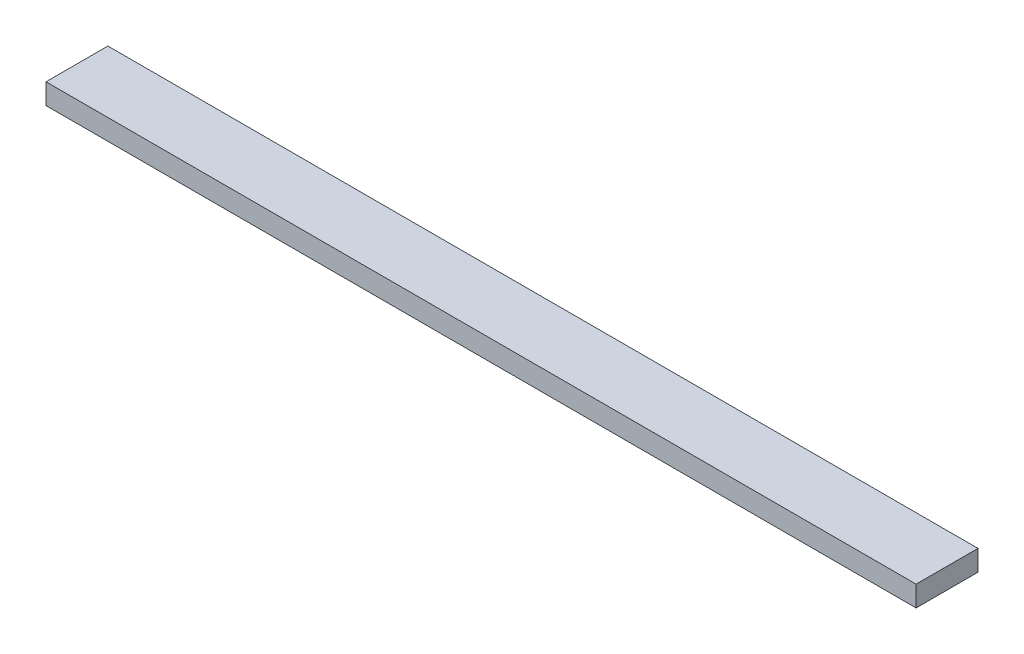
SolidWorks part; units mm, degrees
material "ABS"
ref_plane "Front Plane" through (0, 0, 0) normal (0, 0, 1) x (1, 0, 0)
ref_plane "Top Plane" through (0, 0, 0) normal (0, 1, 0) x (1, 0, 0)
ref_plane "Right Plane" through (0, 0, 0) normal (1, 0, 0) x (0, 0, -1)
sketch "Sketch1" plane through (0, 0, 0) normal (0, 0, 1) x (1, 0, 0)
  line L0 (5.5, 0) -> (-5.5, 0) construction
  line L1 (-77.8319, 4) -> (77.8319, 4)
  line L2 (-77.8319, 4) -> (-77.8319, 0)
  line L3 (-77.8319, 0) -> (77.8319, 0)
  line L4 (77.8319, 4) -> (77.8319, 0)
  line L5 (0, -9.2078) -> (0, 9.2078) construction
extrude "Boss-Extrude1" add sketch "Sketch1" along normal blind 10
sketch "Sketch2" plane through (0, 0, 0) normal (0, 0, 1) x (1, 0, 0)
  line L0 (-65.3126, 4) -> (-63.6747, 8.5)
  line L1 (77.8319, 4) -> (-77.8319, 4) construction
  line L2 (-63.6747, 8.5) -> (-61.989, 8.5)
  line L3 (-61.989, 8.5) -> (-60.3511, 4)
  line L4 (-65.3126, 4) -> (-60.3511, 4)
  line L5 (0, -9.2078) -> (0, 9.2078) construction
  line L6 (-62.8319, 8.5) -> (-62.8319, 4) construction
  line L9 (-34.7801, 6.5) -> (34.9733, 6.5) construction
  point P18 (-61.2611, 6.5)
  point P19 (-64.4026, 6.5)
extrude "Boss-Extrude4" add sketch "Sketch2" along normal up to surface (10 mm away) up to face at (0, 2, 10)
fillet "Fillet1" radius 0.5 2 edges
pattern_linear "LPattern1" count 21 spacing 6.2832 along (1, 0, 0) of "Boss-Extrude4", "Fillet1"
hole_wizard "CSK for M4 Hex Socket Countersunk Cap Screw1" positions "Sketch7" profile "Sketch6" countersink size "M4" standard "ISO"
sketch "Sketch7" plane through (0, 4, 0) normal (0, 1, 0) x (1, 0, 0)
  line L0 (-77.8319, -10) -> (-77.8319, 0) construction
  line L1 (77.8319, -10) -> (77.8319, 0) construction
  line L2 (-4.5728, 0) -> (4.5728, 0) construction
  point P0 (-71.8319, -5)
  point P2 (71.8319, -5)
sketch "Sketch6" plane through (-71.8319, 4, 5) normal (1, 0, 0) x (0, 0, 1)
  line L0 (0, 0) -> (0, 4)
  line L1 (0, 4) -> (2.25, 4)
  line L2 (2.25, 4) -> (2.25, 2.23)
  line L3 (2.25, 2.23) -> (4.48, 0)
  line L5 (4.48, 0) -> (0, 0)
  line L6 (-2.25, 2.23) -> (-4.48, 0) construction
  line L11 (0, -6.35) -> (0, 107.95) construction
  dimension "Thru Hole Dia." = 4.5
  dimension "Thru Hole Depth" = 4
  dimension "Near C'Sink Dia." = 8.96
  dimension "Near C'Sink Angle" = 90
ref_plane "Plane1" through (0, 26.5, 0) normal (0, 1, 0) x (1, 0, 0)
sketch "Sketch8" [suppressed] plane through (0, 0, 0) normal (0, -1, 0) x (1, 0, 0)
  line L4 (-77.8319, 0) -> (77.8319, 0)
  line L5 (77.8319, 0) -> (77.8319, 10)
  line L6 (77.8319, 10) -> (-77.8319, 10)
  line L7 (-77.8319, 10) -> (-77.8319, 0)
  line L8 (-77.8319, 0) -> (77.8319, 0)
  line L9 (77.8319, 0) -> (77.8319, 10)
  line L10 (77.8319, 10) -> (-77.8319, 10)
  line L11 (-77.8319, 10) -> (-77.8319, 0)
  circle A0 centre (-71.8319, 5) radius 2.25 construction
  circle A1 centre (-71.8319, 5) radius 2.25
  dimension "D1" = 0
extrude "Boss-Extrude5" [suppressed] add sketch "Sketch8" along normal blind 30
sketch "Sketch9" plane through (0, 0, 10) normal (0, 0, 1) x (1, 0, 0)
  line L88 (-77.8319, 4) -> (-77.8319, 0)
  line L89 (-77.8319, 0) -> (77.8319, 0)
  line L90 (-77.8319, 4) -> (-77.8319, 0)
  line L91 (77.8319, 4) -> (65.6627, 4)
  line L92 (65.1928, 4.329) -> (63.6747, 8.5)
  line L93 (63.6747, 8.5) -> (61.989, 8.5)
  line L94 (61.989, 8.5) -> (60.4709, 4.329)
  line L95 (60.001, 4) -> (59.3795, 4)
  line L96 (58.9096, 4.329) -> (57.3915, 8.5)
  line L97 (57.3915, 8.5) -> (55.7058, 8.5)
  line L98 (55.7058, 8.5) -> (54.1877, 4.329)
  line L99 (53.7178, 4) -> (53.0963, 4)
  line L100 (52.6265, 4.329) -> (51.1083, 8.5)
  line L101 (51.1083, 8.5) -> (49.4226, 8.5)
  line L102 (49.4226, 8.5) -> (47.9045, 4.329)
  line L103 (47.4347, 4) -> (46.8131, 4)
  line L104 (46.3433, 4.329) -> (44.8252, 8.5)
  line L105 (44.8252, 8.5) -> (43.1394, 8.5)
  line L106 (43.1394, 8.5) -> (41.6213, 4.329)
  line L107 (41.1515, 4) -> (40.5299, 4)
  line L108 (40.0601, 4.329) -> (38.542, 8.5)
  line L109 (38.542, 8.5) -> (36.8563, 8.5)
  line L110 (36.8563, 8.5) -> (35.3381, 4.329)
  line L111 (34.8683, 4) -> (34.2468, 4)
  line L112 (33.7769, 4.329) -> (32.2588, 8.5)
  line L113 (32.2588, 8.5) -> (30.5731, 8.5)
  line L114 (30.5731, 8.5) -> (29.0549, 4.329)
  line L115 (28.5851, 4) -> (27.9636, 4)
  line L116 (27.4937, 4.329) -> (25.9756, 8.5)
  line L117 (25.9756, 8.5) -> (24.2899, 8.5)
  line L118 (24.2899, 8.5) -> (22.7718, 4.329)
  line L119 (22.3019, 4) -> (21.6804, 4)
  line L120 (21.2105, 4.329) -> (19.6924, 8.5)
  line L121 (19.6924, 8.5) -> (18.0067, 8.5)
  line L122 (18.0067, 8.5) -> (16.4886, 4.329)
  line L123 (16.0187, 4) -> (15.3972, 4)
  line L124 (14.9273, 4.329) -> (13.4092, 8.5)
  line L125 (13.4092, 8.5) -> (11.7235, 8.5)
  line L126 (11.7235, 8.5) -> (10.2054, 4.329)
  line L127 (9.7355, 4) -> (9.114, 4)
  line L128 (8.6442, 4.329) -> (7.126, 8.5)
  line L129 (7.126, 8.5) -> (5.4403, 8.5)
  line L130 (5.4403, 8.5) -> (3.9222, 4.329)
  line L131 (3.4524, 4) -> (2.8308, 4)
  line L132 (2.361, 4.329) -> (0.8429, 8.5)
  line L133 (0.8429, 8.5) -> (-0.8429, 8.5)
  line L134 (-0.8429, 8.5) -> (-2.361, 4.329)
  line L135 (-2.8308, 4) -> (-3.4524, 4)
  line L136 (-3.9222, 4.329) -> (-5.4403, 8.5)
  line L137 (-5.4403, 8.5) -> (-7.126, 8.5)
  line L138 (-7.126, 8.5) -> (-8.6442, 4.329)
  line L139 (-9.114, 4) -> (-9.7355, 4)
  line L140 (-10.2054, 4.329) -> (-11.7235, 8.5)
  line L141 (-11.7235, 8.5) -> (-13.4092, 8.5)
  line L142 (-13.4092, 8.5) -> (-14.9273, 4.329)
  line L143 (-15.3972, 4) -> (-16.0187, 4)
  line L144 (-16.4886, 4.329) -> (-18.0067, 8.5)
  line L145 (-18.0067, 8.5) -> (-19.6924, 8.5)
  line L146 (-19.6924, 8.5) -> (-21.2105, 4.329)
  line L147 (-21.6804, 4) -> (-22.3019, 4)
  line L148 (-22.7718, 4.329) -> (-24.2899, 8.5)
  line L149 (-24.2899, 8.5) -> (-25.9756, 8.5)
  line L150 (-25.9756, 8.5) -> (-27.4937, 4.329)
  line L151 (-27.9636, 4) -> (-28.5851, 4)
  line L152 (-29.0549, 4.329) -> (-30.5731, 8.5)
  line L153 (-30.5731, 8.5) -> (-32.2588, 8.5)
  line L154 (-32.2588, 8.5) -> (-33.7769, 4.329)
  line L155 (-34.2468, 4) -> (-34.8683, 4)
  line L156 (-35.3381, 4.329) -> (-36.8563, 8.5)
  line L157 (-36.8563, 8.5) -> (-38.542, 8.5)
  line L158 (-38.542, 8.5) -> (-40.0601, 4.329)
  line L159 (-40.5299, 4) -> (-41.1515, 4)
  line L160 (-41.6213, 4.329) -> (-43.1394, 8.5)
  line L161 (-43.1394, 8.5) -> (-44.8252, 8.5)
  line L162 (-44.8252, 8.5) -> (-46.3433, 4.329)
  line L163 (-46.8131, 4) -> (-47.4347, 4)
  line L164 (-47.9045, 4.329) -> (-49.4226, 8.5)
  line L165 (-49.4226, 8.5) -> (-51.1083, 8.5)
  line L166 (-51.1083, 8.5) -> (-52.6265, 4.329)
  line L167 (-53.0963, 4) -> (-53.7178, 4)
  line L168 (-54.1877, 4.329) -> (-55.7058, 8.5)
  line L169 (-55.7058, 8.5) -> (-57.3915, 8.5)
  line L170 (-57.3915, 8.5) -> (-58.9096, 4.329)
  line L171 (-59.3795, 4) -> (-60.001, 4)
  line L172 (-60.4709, 4.329) -> (-61.989, 8.5)
  line L173 (-61.989, 8.5) -> (-63.6747, 8.5)
  line L174 (-63.6747, 8.5) -> (-65.1928, 4.329)
  line L175 (-65.6627, 4) -> (-77.8319, 4)
  line L176 (77.8319, 0) -> (77.8319, 4)
  line L177 (-77.8319, 0) -> (77.8319, 0)
  line L178 (77.8319, 0) -> (77.8319, 4)
  line L179 (77.8319, 4) -> (65.6627, 4)
  line L180 (65.1928, 4.329) -> (63.6747, 8.5)
  line L181 (63.6747, 8.5) -> (61.989, 8.5)
  line L182 (61.989, 8.5) -> (60.4709, 4.329)
  line L183 (60.001, 4) -> (59.3795, 4)
  line L184 (58.9096, 4.329) -> (57.3915, 8.5)
  line L185 (57.3915, 8.5) -> (55.7058, 8.5)
  line L186 (55.7058, 8.5) -> (54.1877, 4.329)
  line L187 (53.7178, 4) -> (53.0963, 4)
  line L188 (52.6265, 4.329) -> (51.1083, 8.5)
  line L189 (51.1083, 8.5) -> (49.4226, 8.5)
  line L190 (49.4226, 8.5) -> (47.9045, 4.329)
  line L191 (47.4347, 4) -> (46.8131, 4)
  line L192 (46.3433, 4.329) -> (44.8252, 8.5)
  line L193 (44.8252, 8.5) -> (43.1394, 8.5)
  line L194 (43.1394, 8.5) -> (41.6213, 4.329)
  line L195 (41.1515, 4) -> (40.5299, 4)
  line L196 (40.0601, 4.329) -> (38.542, 8.5)
  line L197 (38.542, 8.5) -> (36.8563, 8.5)
  line L198 (36.8563, 8.5) -> (35.3381, 4.329)
  line L199 (34.8683, 4) -> (34.2468, 4)
  line L200 (33.7769, 4.329) -> (32.2588, 8.5)
  line L201 (32.2588, 8.5) -> (30.5731, 8.5)
  line L202 (30.5731, 8.5) -> (29.0549, 4.329)
  line L203 (28.5851, 4) -> (27.9636, 4)
  line L204 (27.4937, 4.329) -> (25.9756, 8.5)
  line L205 (25.9756, 8.5) -> (24.2899, 8.5)
  line L206 (24.2899, 8.5) -> (22.7718, 4.329)
  line L207 (22.3019, 4) -> (21.6804, 4)
  line L208 (21.2105, 4.329) -> (19.6924, 8.5)
  line L209 (19.6924, 8.5) -> (18.0067, 8.5)
  line L210 (18.0067, 8.5) -> (16.4886, 4.329)
  line L211 (16.0187, 4) -> (15.3972, 4)
  line L212 (14.9273, 4.329) -> (13.4092, 8.5)
  line L213 (13.4092, 8.5) -> (11.7235, 8.5)
  line L214 (11.7235, 8.5) -> (10.2054, 4.329)
  line L215 (9.7355, 4) -> (9.114, 4)
  line L216 (8.6442, 4.329) -> (7.126, 8.5)
  line L217 (7.126, 8.5) -> (5.4403, 8.5)
  line L218 (5.4403, 8.5) -> (3.9222, 4.329)
  line L219 (3.4524, 4) -> (2.8308, 4)
  line L220 (2.361, 4.329) -> (0.8429, 8.5)
  line L221 (0.8429, 8.5) -> (-0.8429, 8.5)
  line L222 (-0.8429, 8.5) -> (-2.361, 4.329)
  line L223 (-2.8308, 4) -> (-3.4524, 4)
  line L224 (-3.9222, 4.329) -> (-5.4403, 8.5)
  line L225 (-5.4403, 8.5) -> (-7.126, 8.5)
  line L226 (-7.126, 8.5) -> (-8.6442, 4.329)
  line L227 (-9.114, 4) -> (-9.7355, 4)
  line L228 (-10.2054, 4.329) -> (-11.7235, 8.5)
  line L229 (-11.7235, 8.5) -> (-13.4092, 8.5)
  line L230 (-13.4092, 8.5) -> (-14.9273, 4.329)
  line L231 (-15.3972, 4) -> (-16.0187, 4)
  line L232 (-16.4886, 4.329) -> (-18.0067, 8.5)
  line L233 (-18.0067, 8.5) -> (-19.6924, 8.5)
  line L234 (-19.6924, 8.5) -> (-21.2105, 4.329)
  line L235 (-21.6804, 4) -> (-22.3019, 4)
  line L236 (-22.7718, 4.329) -> (-24.2899, 8.5)
  line L237 (-24.2899, 8.5) -> (-25.9756, 8.5)
  line L238 (-25.9756, 8.5) -> (-27.4937, 4.329)
  line L239 (-27.9636, 4) -> (-28.5851, 4)
  line L240 (-29.0549, 4.329) -> (-30.5731, 8.5)
  line L241 (-30.5731, 8.5) -> (-32.2588, 8.5)
  line L242 (-32.2588, 8.5) -> (-33.7769, 4.329)
  line L243 (-34.2468, 4) -> (-34.8683, 4)
  line L244 (-35.3381, 4.329) -> (-36.8563, 8.5)
  line L245 (-36.8563, 8.5) -> (-38.542, 8.5)
  line L246 (-38.542, 8.5) -> (-40.0601, 4.329)
  line L247 (-40.5299, 4) -> (-41.1515, 4)
  line L248 (-41.6213, 4.329) -> (-43.1394, 8.5)
  line L249 (-43.1394, 8.5) -> (-44.8252, 8.5)
  line L250 (-44.8252, 8.5) -> (-46.3433, 4.329)
  line L251 (-46.8131, 4) -> (-47.4347, 4)
  line L252 (-47.9045, 4.329) -> (-49.4226, 8.5)
  line L253 (-49.4226, 8.5) -> (-51.1083, 8.5)
  line L254 (-51.1083, 8.5) -> (-52.6265, 4.329)
  line L255 (-53.0963, 4) -> (-53.7178, 4)
  line L256 (-54.1877, 4.329) -> (-55.7058, 8.5)
  line L257 (-55.7058, 8.5) -> (-57.3915, 8.5)
  line L258 (-57.3915, 8.5) -> (-58.9096, 4.329)
  line L259 (-59.3795, 4) -> (-60.001, 4)
  line L260 (-60.4709, 4.329) -> (-61.989, 8.5)
  line L261 (-61.989, 8.5) -> (-63.6747, 8.5)
  line L262 (-63.6747, 8.5) -> (-65.1928, 4.329)
  line L263 (-65.6627, 4) -> (-77.8319, 4)
  arc A42 (65.1928, 4.329) -> (65.6627, 4) centre (65.6627, 4.5) ccw
  arc A43 (60.001, 4) -> (60.4709, 4.329) centre (60.001, 4.5) ccw
  arc A44 (58.9096, 4.329) -> (59.3795, 4) centre (59.3795, 4.5) ccw
  arc A45 (53.7178, 4) -> (54.1877, 4.329) centre (53.7178, 4.5) ccw
  arc A46 (52.6265, 4.329) -> (53.0963, 4) centre (53.0963, 4.5) ccw
  arc A47 (47.4347, 4) -> (47.9045, 4.329) centre (47.4347, 4.5) ccw
  arc A48 (46.3433, 4.329) -> (46.8131, 4) centre (46.8131, 4.5) ccw
  arc A49 (41.1515, 4) -> (41.6213, 4.329) centre (41.1515, 4.5) ccw
  arc A50 (40.0601, 4.329) -> (40.5299, 4) centre (40.5299, 4.5) ccw
  arc A51 (34.8683, 4) -> (35.3381, 4.329) centre (34.8683, 4.5) ccw
  arc A52 (33.7769, 4.329) -> (34.2468, 4) centre (34.2468, 4.5) ccw
  arc A53 (28.5851, 4) -> (29.0549, 4.329) centre (28.5851, 4.5) ccw
  arc A54 (27.4937, 4.329) -> (27.9636, 4) centre (27.9636, 4.5) ccw
  arc A55 (22.3019, 4) -> (22.7718, 4.329) centre (22.3019, 4.5) ccw
  arc A56 (21.2105, 4.329) -> (21.6804, 4) centre (21.6804, 4.5) ccw
  arc A57 (16.0187, 4) -> (16.4886, 4.329) centre (16.0187, 4.5) ccw
  arc A58 (14.9273, 4.329) -> (15.3972, 4) centre (15.3972, 4.5) ccw
  arc A59 (9.7355, 4) -> (10.2054, 4.329) centre (9.7355, 4.5) ccw
  arc A60 (8.6442, 4.329) -> (9.114, 4) centre (9.114, 4.5) ccw
  arc A61 (3.4524, 4) -> (3.9222, 4.329) centre (3.4524, 4.5) ccw
  arc A62 (2.361, 4.329) -> (2.8308, 4) centre (2.8308, 4.5) ccw
  arc A63 (-2.8308, 4) -> (-2.361, 4.329) centre (-2.8308, 4.5) ccw
  arc A64 (-3.9222, 4.329) -> (-3.4524, 4) centre (-3.4524, 4.5) ccw
  arc A65 (-9.114, 4) -> (-8.6442, 4.329) centre (-9.114, 4.5) ccw
  arc A66 (-10.2054, 4.329) -> (-9.7355, 4) centre (-9.7355, 4.5) ccw
  arc A67 (-15.3972, 4) -> (-14.9273, 4.329) centre (-15.3972, 4.5) ccw
  arc A68 (-16.4886, 4.329) -> (-16.0187, 4) centre (-16.0187, 4.5) ccw
  arc A69 (-21.6804, 4) -> (-21.2105, 4.329) centre (-21.6804, 4.5) ccw
  arc A70 (-22.7718, 4.329) -> (-22.3019, 4) centre (-22.3019, 4.5) ccw
  arc A71 (-27.9636, 4) -> (-27.4937, 4.329) centre (-27.9636, 4.5) ccw
  arc A72 (-29.0549, 4.329) -> (-28.5851, 4) centre (-28.5851, 4.5) ccw
  arc A73 (-34.2468, 4) -> (-33.7769, 4.329) centre (-34.2468, 4.5) ccw
  arc A74 (-35.3381, 4.329) -> (-34.8683, 4) centre (-34.8683, 4.5) ccw
  arc A75 (-40.5299, 4) -> (-40.0601, 4.329) centre (-40.5299, 4.5) ccw
  arc A76 (-41.6213, 4.329) -> (-41.1515, 4) centre (-41.1515, 4.5) ccw
  arc A77 (-46.8131, 4) -> (-46.3433, 4.329) centre (-46.8131, 4.5) ccw
  arc A78 (-47.9045, 4.329) -> (-47.4347, 4) centre (-47.4347, 4.5) ccw
  arc A79 (-53.0963, 4) -> (-52.6265, 4.329) centre (-53.0963, 4.5) ccw
  arc A80 (-54.1877, 4.329) -> (-53.7178, 4) centre (-53.7178, 4.5) ccw
  arc A81 (-59.3795, 4) -> (-58.9096, 4.329) centre (-59.3795, 4.5) ccw
  arc A82 (-60.4709, 4.329) -> (-60.001, 4) centre (-60.001, 4.5) ccw
  arc A83 (-65.6627, 4) -> (-65.1928, 4.329) centre (-65.6627, 4.5) ccw
  arc A84 (65.1928, 4.329) -> (65.6627, 4) centre (65.6627, 4.5) ccw
  arc A85 (60.001, 4) -> (60.4709, 4.329) centre (60.001, 4.5) ccw
  arc A86 (58.9096, 4.329) -> (59.3795, 4) centre (59.3795, 4.5) ccw
  arc A87 (53.7178, 4) -> (54.1877, 4.329) centre (53.7178, 4.5) ccw
  arc A88 (52.6265, 4.329) -> (53.0963, 4) centre (53.0963, 4.5) ccw
  arc A89 (47.4347, 4) -> (47.9045, 4.329) centre (47.4347, 4.5) ccw
  arc A90 (46.3433, 4.329) -> (46.8131, 4) centre (46.8131, 4.5) ccw
  arc A91 (41.1515, 4) -> (41.6213, 4.329) centre (41.1515, 4.5) ccw
  arc A92 (40.0601, 4.329) -> (40.5299, 4) centre (40.5299, 4.5) ccw
  arc A93 (34.8683, 4) -> (35.3381, 4.329) centre (34.8683, 4.5) ccw
  arc A94 (33.7769, 4.329) -> (34.2468, 4) centre (34.2468, 4.5) ccw
  arc A95 (28.5851, 4) -> (29.0549, 4.329) centre (28.5851, 4.5) ccw
  arc A96 (27.4937, 4.329) -> (27.9636, 4) centre (27.9636, 4.5) ccw
  arc A97 (22.3019, 4) -> (22.7718, 4.329) centre (22.3019, 4.5) ccw
  arc A98 (21.2105, 4.329) -> (21.6804, 4) centre (21.6804, 4.5) ccw
  arc A99 (16.0187, 4) -> (16.4886, 4.329) centre (16.0187, 4.5) ccw
  arc A100 (14.9273, 4.329) -> (15.3972, 4) centre (15.3972, 4.5) ccw
  arc A101 (9.7355, 4) -> (10.2054, 4.329) centre (9.7355, 4.5) ccw
  arc A102 (8.6442, 4.329) -> (9.114, 4) centre (9.114, 4.5) ccw
  arc A103 (3.4524, 4) -> (3.9222, 4.329) centre (3.4524, 4.5) ccw
  arc A104 (2.361, 4.329) -> (2.8308, 4) centre (2.8308, 4.5) ccw
  arc A105 (-2.8308, 4) -> (-2.361, 4.329) centre (-2.8308, 4.5) ccw
  arc A106 (-3.9222, 4.329) -> (-3.4524, 4) centre (-3.4524, 4.5) ccw
  arc A107 (-9.114, 4) -> (-8.6442, 4.329) centre (-9.114, 4.5) ccw
  arc A108 (-10.2054, 4.329) -> (-9.7355, 4) centre (-9.7355, 4.5) ccw
  arc A109 (-15.3972, 4) -> (-14.9273, 4.329) centre (-15.3972, 4.5) ccw
  arc A110 (-16.4886, 4.329) -> (-16.0187, 4) centre (-16.0187, 4.5) ccw
  arc A111 (-21.6804, 4) -> (-21.2105, 4.329) centre (-21.6804, 4.5) ccw
  arc A112 (-22.7718, 4.329) -> (-22.3019, 4) centre (-22.3019, 4.5) ccw
  arc A113 (-27.9636, 4) -> (-27.4937, 4.329) centre (-27.9636, 4.5) ccw
  arc A114 (-29.0549, 4.329) -> (-28.5851, 4) centre (-28.5851, 4.5) ccw
  arc A115 (-34.2468, 4) -> (-33.7769, 4.329) centre (-34.2468, 4.5) ccw
  arc A116 (-35.3381, 4.329) -> (-34.8683, 4) centre (-34.8683, 4.5) ccw
  arc A117 (-40.5299, 4) -> (-40.0601, 4.329) centre (-40.5299, 4.5) ccw
  arc A118 (-41.6213, 4.329) -> (-41.1515, 4) centre (-41.1515, 4.5) ccw
  arc A119 (-46.8131, 4) -> (-46.3433, 4.329) centre (-46.8131, 4.5) ccw
  arc A120 (-47.9045, 4.329) -> (-47.4347, 4) centre (-47.4347, 4.5) ccw
  arc A121 (-53.0963, 4) -> (-52.6265, 4.329) centre (-53.0963, 4.5) ccw
  arc A122 (-54.1877, 4.329) -> (-53.7178, 4) centre (-53.7178, 4.5) ccw
  arc A123 (-59.3795, 4) -> (-58.9096, 4.329) centre (-59.3795, 4.5) ccw
  arc A124 (-60.4709, 4.329) -> (-60.001, 4) centre (-60.001, 4.5) ccw
  arc A125 (-65.6627, 4) -> (-65.1928, 4.329) centre (-65.6627, 4.5) ccw
  dimension "D1" = 0
extrude "Boss-Extrude6" add sketch "Sketch9" along normal blind 6 contours L262 A125 L263 L90 L177 L178 L179 A84 L180 L181 L182 A85 L183 A86 L184 L185 L186 A87 L187 A88 L188 L189 L190 A89 L191 A90 L192 L193 L194 A91 L195 A92 L196 L197 L198 A93 L199 A94 L200 L201 L202 A95 L203 A96 L204 L205 L206 A97 L207 A98 L208 L209 L210 A99 L211 A100 L212 L213 L214 A101 L215 A102 L216 L217 L218 A103 L219 A104 L220 L221 L222 A105 L223 A106 L224 L225 L226 A107 L227 A108 L228 L229 L230 A109 L231 A110 L232 L233 L234 A111 L235 A112 L236 L237 L238 A113 L239 A114 L240 L241 L242 A115 L243 A116 L244 L245 L246 A117 L247 A118 L248 L249 L250 A119 L251 A120 L252 L253 L254 A121 L255 A122 L256 L257 L258 A123 L259 A124 L260 L261
sketch "Sketch10" [suppressed] plane through (0, 0, 16) normal (0, 0, 1) x (1, 0, 0)
  line L0 (-49.4226, 8.5) -> (-51.1083, 8.5) construction
  line L1 (-77.8319, -30) -> (90.1846, -30)
  line L2 (-77.8319, -30) -> (-77.8319, -7.5)
  line L3 (-77.8319, -7.5) -> (90.1846, -7.5)
  line L4 (90.1846, -30) -> (90.1846, -7.5)
  dimension "D1" = 16
extrude "Cut-Extrude1" [suppressed] cut sketch "Sketch10" against normal blind 40
sketch "Sketch11" plane through (-77.8319, 0, 0) normal (-1, 0, 0) x (0, 0, 1)
  line L4 (0, 4) -> (0, 0)
  line L5 (0, 0) -> (16, 0)
  line L6 (16, 0) -> (16, 4)
  line L7 (16, 4) -> (0, 4)
  line L8 (0, 4) -> (0, 0)
  line L9 (0, 0) -> (16, 0)
  line L10 (16, 0) -> (16, 4)
  line L11 (16, 4) -> (0, 4)
  dimension "D1" = 0
extrude "Boss-Extrude8" add sketch "Sketch11" along normal blind 10
sketch "Sketch12" plane through (77.8319, 0, 0) normal (1, 0, 0) x (0, 0, -1)
  line L4 (-16, 4) -> (-16, 0)
  line L5 (-16, 0) -> (0, 0)
  line L6 (0, 0) -> (0, 4)
  line L7 (0, 4) -> (-16, 4)
  line L8 (-16, 4) -> (-16, 0)
  line L9 (-16, 0) -> (0, 0)
  line L10 (0, 0) -> (0, 4)
  line L11 (0, 4) -> (-16, 4)
  dimension "D1" = 0
extrude "Boss-Extrude9" add sketch "Sketch12" along normal blind 10
sketch "Sketch15" plane through (0, 0, 0) normal (0, -1, 0) x (1, 0, 0)
  line L4 (-87.8319, 0) -> (87.8319, 0)
  line L5 (87.8319, 0) -> (87.8319, 16)
  line L6 (87.8319, 16) -> (-87.8319, 16)
  line L7 (-87.8319, 16) -> (-87.8319, 0)
  line L8 (-87.8319, 0) -> (87.8319, 0)
  line L9 (87.8319, 0) -> (87.8319, 16)
  line L10 (87.8319, 16) -> (-87.8319, 16)
  line L11 (-87.8319, 16) -> (-87.8319, 0)
  dimension "D1" = 0
extrude "Boss-Extrude10" add sketch "Sketch15" along normal blind 5
sketch "Sketch16" plane through (0, 0, 16) normal (0, 0, 1) x (1, 0, 0)
  line L88 (-61.989, 8.5) -> (-63.6747, 8.5)
  line L89 (-63.6747, 8.5) -> (-65.1928, 4.329)
  line L90 (-65.6627, 4) -> (-87.8319, 4)
  line L91 (-87.8319, 4) -> (-87.8319, -5)
  line L92 (-87.8319, -5) -> (87.8319, -5)
  line L93 (87.8319, -5) -> (87.8319, 4)
  line L94 (87.8319, 4) -> (65.6627, 4)
  line L95 (65.1928, 4.329) -> (63.6747, 8.5)
  line L96 (63.6747, 8.5) -> (61.989, 8.5)
  line L97 (61.989, 8.5) -> (60.4709, 4.329)
  line L98 (60.001, 4) -> (59.3795, 4)
  line L99 (58.9096, 4.329) -> (57.3915, 8.5)
  line L100 (57.3915, 8.5) -> (55.7058, 8.5)
  line L101 (55.7058, 8.5) -> (54.1877, 4.329)
  line L102 (53.7178, 4) -> (53.0963, 4)
  line L103 (52.6265, 4.329) -> (51.1083, 8.5)
  line L104 (51.1083, 8.5) -> (49.4226, 8.5)
  line L105 (49.4226, 8.5) -> (47.9045, 4.329)
  line L106 (47.4347, 4) -> (46.8131, 4)
  line L107 (46.3433, 4.329) -> (44.8252, 8.5)
  line L108 (44.8252, 8.5) -> (43.1394, 8.5)
  line L109 (43.1394, 8.5) -> (41.6213, 4.329)
  line L110 (41.1515, 4) -> (40.5299, 4)
  line L111 (40.0601, 4.329) -> (38.542, 8.5)
  line L112 (38.542, 8.5) -> (36.8563, 8.5)
  line L113 (36.8563, 8.5) -> (35.3381, 4.329)
  line L114 (34.8683, 4) -> (34.2468, 4)
  line L115 (33.7769, 4.329) -> (32.2588, 8.5)
  line L116 (32.2588, 8.5) -> (30.5731, 8.5)
  line L117 (30.5731, 8.5) -> (29.0549, 4.329)
  line L118 (28.5851, 4) -> (27.9636, 4)
  line L119 (27.4937, 4.329) -> (25.9756, 8.5)
  line L120 (25.9756, 8.5) -> (24.2899, 8.5)
  line L121 (24.2899, 8.5) -> (22.7718, 4.329)
  line L122 (22.3019, 4) -> (21.6804, 4)
  line L123 (21.2105, 4.329) -> (19.6924, 8.5)
  line L124 (19.6924, 8.5) -> (18.0067, 8.5)
  line L125 (18.0067, 8.5) -> (16.4886, 4.329)
  line L126 (16.0187, 4) -> (15.3972, 4)
  line L127 (14.9273, 4.329) -> (13.4092, 8.5)
  line L128 (13.4092, 8.5) -> (11.7235, 8.5)
  line L129 (11.7235, 8.5) -> (10.2054, 4.329)
  line L130 (9.7355, 4) -> (9.114, 4)
  line L131 (8.6442, 4.329) -> (7.126, 8.5)
  line L132 (7.126, 8.5) -> (5.4403, 8.5)
  line L133 (5.4403, 8.5) -> (3.9222, 4.329)
  line L134 (3.4524, 4) -> (2.8308, 4)
  line L135 (2.361, 4.329) -> (0.8429, 8.5)
  line L136 (0.8429, 8.5) -> (-0.8429, 8.5)
  line L137 (-0.8429, 8.5) -> (-2.361, 4.329)
  line L138 (-2.8308, 4) -> (-3.4524, 4)
  line L139 (-3.9222, 4.329) -> (-5.4403, 8.5)
  line L140 (-5.4403, 8.5) -> (-7.126, 8.5)
  line L141 (-7.126, 8.5) -> (-8.6442, 4.329)
  line L142 (-9.114, 4) -> (-9.7355, 4)
  line L143 (-10.2054, 4.329) -> (-11.7235, 8.5)
  line L144 (-11.7235, 8.5) -> (-13.4092, 8.5)
  line L145 (-13.4092, 8.5) -> (-14.9273, 4.329)
  line L146 (-15.3972, 4) -> (-16.0187, 4)
  line L147 (-16.4886, 4.329) -> (-18.0067, 8.5)
  line L148 (-18.0067, 8.5) -> (-19.6924, 8.5)
  line L149 (-19.6924, 8.5) -> (-21.2105, 4.329)
  line L150 (-21.6804, 4) -> (-22.3019, 4)
  line L151 (-22.7718, 4.329) -> (-24.2899, 8.5)
  line L152 (-24.2899, 8.5) -> (-25.9756, 8.5)
  line L153 (-25.9756, 8.5) -> (-27.4937, 4.329)
  line L154 (-27.9636, 4) -> (-28.5851, 4)
  line L155 (-29.0549, 4.329) -> (-30.5731, 8.5)
  line L156 (-30.5731, 8.5) -> (-32.2588, 8.5)
  line L157 (-32.2588, 8.5) -> (-33.7769, 4.329)
  line L158 (-34.2468, 4) -> (-34.8683, 4)
  line L159 (-35.3381, 4.329) -> (-36.8563, 8.5)
  line L160 (-36.8563, 8.5) -> (-38.542, 8.5)
  line L161 (-38.542, 8.5) -> (-40.0601, 4.329)
  line L162 (-40.5299, 4) -> (-41.1515, 4)
  line L163 (-41.6213, 4.329) -> (-43.1394, 8.5)
  line L164 (-43.1394, 8.5) -> (-44.8252, 8.5)
  line L165 (-44.8252, 8.5) -> (-46.3433, 4.329)
  line L166 (-46.8131, 4) -> (-47.4347, 4)
  line L167 (-47.9045, 4.329) -> (-49.4226, 8.5)
  line L168 (-49.4226, 8.5) -> (-51.1083, 8.5)
  line L169 (-51.1083, 8.5) -> (-52.6265, 4.329)
  line L170 (-53.0963, 4) -> (-53.7178, 4)
  line L171 (-54.1877, 4.329) -> (-55.7058, 8.5)
  line L172 (-55.7058, 8.5) -> (-57.3915, 8.5)
  line L173 (-57.3915, 8.5) -> (-58.9096, 4.329)
  line L174 (-59.3795, 4) -> (-60.001, 4)
  line L175 (-60.4709, 4.329) -> (-61.989, 8.5)
  line L176 (-61.989, 8.5) -> (-63.6747, 8.5)
  line L177 (-63.6747, 8.5) -> (-65.1928, 4.329)
  line L178 (-65.6627, 4) -> (-87.8319, 4)
  line L179 (-87.8319, 4) -> (-87.8319, -5)
  line L180 (-87.8319, -5) -> (87.8319, -5)
  line L181 (87.8319, -5) -> (87.8319, 4)
  line L182 (87.8319, 4) -> (65.6627, 4)
  line L183 (65.1928, 4.329) -> (63.6747, 8.5)
  line L184 (63.6747, 8.5) -> (61.989, 8.5)
  line L185 (61.989, 8.5) -> (60.4709, 4.329)
  line L186 (60.001, 4) -> (59.3795, 4)
  line L187 (58.9096, 4.329) -> (57.3915, 8.5)
  line L188 (57.3915, 8.5) -> (55.7058, 8.5)
  line L189 (55.7058, 8.5) -> (54.1877, 4.329)
  line L190 (53.7178, 4) -> (53.0963, 4)
  line L191 (52.6265, 4.329) -> (51.1083, 8.5)
  line L192 (51.1083, 8.5) -> (49.4226, 8.5)
  line L193 (49.4226, 8.5) -> (47.9045, 4.329)
  line L194 (47.4347, 4) -> (46.8131, 4)
  line L195 (46.3433, 4.329) -> (44.8252, 8.5)
  line L196 (44.8252, 8.5) -> (43.1394, 8.5)
  line L197 (43.1394, 8.5) -> (41.6213, 4.329)
  line L198 (41.1515, 4) -> (40.5299, 4)
  line L199 (40.0601, 4.329) -> (38.542, 8.5)
  line L200 (38.542, 8.5) -> (36.8563, 8.5)
  line L201 (36.8563, 8.5) -> (35.3381, 4.329)
  line L202 (34.8683, 4) -> (34.2468, 4)
  line L203 (33.7769, 4.329) -> (32.2588, 8.5)
  line L204 (32.2588, 8.5) -> (30.5731, 8.5)
  line L205 (30.5731, 8.5) -> (29.0549, 4.329)
  line L206 (28.5851, 4) -> (27.9636, 4)
  line L207 (27.4937, 4.329) -> (25.9756, 8.5)
  line L208 (25.9756, 8.5) -> (24.2899, 8.5)
  line L209 (24.2899, 8.5) -> (22.7718, 4.329)
  line L210 (22.3019, 4) -> (21.6804, 4)
  line L211 (21.2105, 4.329) -> (19.6924, 8.5)
  line L212 (19.6924, 8.5) -> (18.0067, 8.5)
  line L213 (18.0067, 8.5) -> (16.4886, 4.329)
  line L214 (16.0187, 4) -> (15.3972, 4)
  line L215 (14.9273, 4.329) -> (13.4092, 8.5)
  line L216 (13.4092, 8.5) -> (11.7235, 8.5)
  line L217 (11.7235, 8.5) -> (10.2054, 4.329)
  line L218 (9.7355, 4) -> (9.114, 4)
  line L219 (8.6442, 4.329) -> (7.126, 8.5)
  line L220 (7.126, 8.5) -> (5.4403, 8.5)
  line L221 (5.4403, 8.5) -> (3.9222, 4.329)
  line L222 (3.4524, 4) -> (2.8308, 4)
  line L223 (2.361, 4.329) -> (0.8429, 8.5)
  line L224 (0.8429, 8.5) -> (-0.8429, 8.5)
  line L225 (-0.8429, 8.5) -> (-2.361, 4.329)
  line L226 (-2.8308, 4) -> (-3.4524, 4)
  line L227 (-3.9222, 4.329) -> (-5.4403, 8.5)
  line L228 (-5.4403, 8.5) -> (-7.126, 8.5)
  line L229 (-7.126, 8.5) -> (-8.6442, 4.329)
  line L230 (-9.114, 4) -> (-9.7355, 4)
  line L231 (-10.2054, 4.329) -> (-11.7235, 8.5)
  line L232 (-11.7235, 8.5) -> (-13.4092, 8.5)
  line L233 (-13.4092, 8.5) -> (-14.9273, 4.329)
  line L234 (-15.3972, 4) -> (-16.0187, 4)
  line L235 (-16.4886, 4.329) -> (-18.0067, 8.5)
  line L236 (-18.0067, 8.5) -> (-19.6924, 8.5)
  line L237 (-19.6924, 8.5) -> (-21.2105, 4.329)
  line L238 (-21.6804, 4) -> (-22.3019, 4)
  line L239 (-22.7718, 4.329) -> (-24.2899, 8.5)
  line L240 (-24.2899, 8.5) -> (-25.9756, 8.5)
  line L241 (-25.9756, 8.5) -> (-27.4937, 4.329)
  line L242 (-27.9636, 4) -> (-28.5851, 4)
  line L243 (-29.0549, 4.329) -> (-30.5731, 8.5)
  line L244 (-30.5731, 8.5) -> (-32.2588, 8.5)
  line L245 (-32.2588, 8.5) -> (-33.7769, 4.329)
  line L246 (-34.2468, 4) -> (-34.8683, 4)
  line L247 (-35.3381, 4.329) -> (-36.8563, 8.5)
  line L248 (-36.8563, 8.5) -> (-38.542, 8.5)
  line L249 (-38.542, 8.5) -> (-40.0601, 4.329)
  line L250 (-40.5299, 4) -> (-41.1515, 4)
  line L251 (-41.6213, 4.329) -> (-43.1394, 8.5)
  line L252 (-43.1394, 8.5) -> (-44.8252, 8.5)
  line L253 (-44.8252, 8.5) -> (-46.3433, 4.329)
  line L254 (-46.8131, 4) -> (-47.4347, 4)
  line L255 (-47.9045, 4.329) -> (-49.4226, 8.5)
  line L256 (-49.4226, 8.5) -> (-51.1083, 8.5)
  line L257 (-51.1083, 8.5) -> (-52.6265, 4.329)
  line L258 (-53.0963, 4) -> (-53.7178, 4)
  line L259 (-54.1877, 4.329) -> (-55.7058, 8.5)
  line L260 (-55.7058, 8.5) -> (-57.3915, 8.5)
  line L261 (-57.3915, 8.5) -> (-58.9096, 4.329)
  line L262 (-59.3795, 4) -> (-60.001, 4)
  line L263 (-60.4709, 4.329) -> (-61.989, 8.5)
  arc A42 (-65.6627, 4) -> (-65.1928, 4.329) centre (-65.6627, 4.5) ccw
  arc A43 (65.1928, 4.329) -> (65.6627, 4) centre (65.6627, 4.5) ccw
  arc A44 (60.001, 4) -> (60.4709, 4.329) centre (60.001, 4.5) ccw
  arc A45 (58.9096, 4.329) -> (59.3795, 4) centre (59.3795, 4.5) ccw
  arc A46 (53.7178, 4) -> (54.1877, 4.329) centre (53.7178, 4.5) ccw
  arc A47 (52.6265, 4.329) -> (53.0963, 4) centre (53.0963, 4.5) ccw
  arc A48 (47.4347, 4) -> (47.9045, 4.329) centre (47.4347, 4.5) ccw
  arc A49 (46.3433, 4.329) -> (46.8131, 4) centre (46.8131, 4.5) ccw
  arc A50 (41.1515, 4) -> (41.6213, 4.329) centre (41.1515, 4.5) ccw
  arc A51 (40.0601, 4.329) -> (40.5299, 4) centre (40.5299, 4.5) ccw
  arc A52 (34.8683, 4) -> (35.3381, 4.329) centre (34.8683, 4.5) ccw
  arc A53 (33.7769, 4.329) -> (34.2468, 4) centre (34.2468, 4.5) ccw
  arc A54 (28.5851, 4) -> (29.0549, 4.329) centre (28.5851, 4.5) ccw
  arc A55 (27.4937, 4.329) -> (27.9636, 4) centre (27.9636, 4.5) ccw
  arc A56 (22.3019, 4) -> (22.7718, 4.329) centre (22.3019, 4.5) ccw
  arc A57 (21.2105, 4.329) -> (21.6804, 4) centre (21.6804, 4.5) ccw
  arc A58 (16.0187, 4) -> (16.4886, 4.329) centre (16.0187, 4.5) ccw
  arc A59 (14.9273, 4.329) -> (15.3972, 4) centre (15.3972, 4.5) ccw
  arc A60 (9.7355, 4) -> (10.2054, 4.329) centre (9.7355, 4.5) ccw
  arc A61 (8.6442, 4.329) -> (9.114, 4) centre (9.114, 4.5) ccw
  arc A62 (3.4524, 4) -> (3.9222, 4.329) centre (3.4524, 4.5) ccw
  arc A63 (2.361, 4.329) -> (2.8308, 4) centre (2.8308, 4.5) ccw
  arc A64 (-2.8308, 4) -> (-2.361, 4.329) centre (-2.8308, 4.5) ccw
  arc A65 (-3.9222, 4.329) -> (-3.4524, 4) centre (-3.4524, 4.5) ccw
  arc A66 (-9.114, 4) -> (-8.6442, 4.329) centre (-9.114, 4.5) ccw
  arc A67 (-10.2054, 4.329) -> (-9.7355, 4) centre (-9.7355, 4.5) ccw
  arc A68 (-15.3972, 4) -> (-14.9273, 4.329) centre (-15.3972, 4.5) ccw
  arc A69 (-16.4886, 4.329) -> (-16.0187, 4) centre (-16.0187, 4.5) ccw
  arc A70 (-21.6804, 4) -> (-21.2105, 4.329) centre (-21.6804, 4.5) ccw
  arc A71 (-22.7718, 4.329) -> (-22.3019, 4) centre (-22.3019, 4.5) ccw
  arc A72 (-27.9636, 4) -> (-27.4937, 4.329) centre (-27.9636, 4.5) ccw
  arc A73 (-29.0549, 4.329) -> (-28.5851, 4) centre (-28.5851, 4.5) ccw
  arc A74 (-34.2468, 4) -> (-33.7769, 4.329) centre (-34.2468, 4.5) ccw
  arc A75 (-35.3381, 4.329) -> (-34.8683, 4) centre (-34.8683, 4.5) ccw
  arc A76 (-40.5299, 4) -> (-40.0601, 4.329) centre (-40.5299, 4.5) ccw
  arc A77 (-41.6213, 4.329) -> (-41.1515, 4) centre (-41.1515, 4.5) ccw
  arc A78 (-46.8131, 4) -> (-46.3433, 4.329) centre (-46.8131, 4.5) ccw
  arc A79 (-47.9045, 4.329) -> (-47.4347, 4) centre (-47.4347, 4.5) ccw
  arc A80 (-53.0963, 4) -> (-52.6265, 4.329) centre (-53.0963, 4.5) ccw
  arc A81 (-54.1877, 4.329) -> (-53.7178, 4) centre (-53.7178, 4.5) ccw
  arc A82 (-59.3795, 4) -> (-58.9096, 4.329) centre (-59.3795, 4.5) ccw
  arc A83 (-60.4709, 4.329) -> (-60.001, 4) centre (-60.001, 4.5) ccw
  arc A84 (-65.6627, 4) -> (-65.1928, 4.329) centre (-65.6627, 4.5) ccw
  arc A85 (65.1928, 4.329) -> (65.6627, 4) centre (65.6627, 4.5) ccw
  arc A86 (60.001, 4) -> (60.4709, 4.329) centre (60.001, 4.5) ccw
  arc A87 (58.9096, 4.329) -> (59.3795, 4) centre (59.3795, 4.5) ccw
  arc A88 (53.7178, 4) -> (54.1877, 4.329) centre (53.7178, 4.5) ccw
  arc A89 (52.6265, 4.329) -> (53.0963, 4) centre (53.0963, 4.5) ccw
  arc A90 (47.4347, 4) -> (47.9045, 4.329) centre (47.4347, 4.5) ccw
  arc A91 (46.3433, 4.329) -> (46.8131, 4) centre (46.8131, 4.5) ccw
  arc A92 (41.1515, 4) -> (41.6213, 4.329) centre (41.1515, 4.5) ccw
  arc A93 (40.0601, 4.329) -> (40.5299, 4) centre (40.5299, 4.5) ccw
  arc A94 (34.8683, 4) -> (35.3381, 4.329) centre (34.8683, 4.5) ccw
  arc A95 (33.7769, 4.329) -> (34.2468, 4) centre (34.2468, 4.5) ccw
  arc A96 (28.5851, 4) -> (29.0549, 4.329) centre (28.5851, 4.5) ccw
  arc A97 (27.4937, 4.329) -> (27.9636, 4) centre (27.9636, 4.5) ccw
  arc A98 (22.3019, 4) -> (22.7718, 4.329) centre (22.3019, 4.5) ccw
  arc A99 (21.2105, 4.329) -> (21.6804, 4) centre (21.6804, 4.5) ccw
  arc A100 (16.0187, 4) -> (16.4886, 4.329) centre (16.0187, 4.5) ccw
  arc A101 (14.9273, 4.329) -> (15.3972, 4) centre (15.3972, 4.5) ccw
  arc A102 (9.7355, 4) -> (10.2054, 4.329) centre (9.7355, 4.5) ccw
  arc A103 (8.6442, 4.329) -> (9.114, 4) centre (9.114, 4.5) ccw
  arc A104 (3.4524, 4) -> (3.9222, 4.329) centre (3.4524, 4.5) ccw
  arc A105 (2.361, 4.329) -> (2.8308, 4) centre (2.8308, 4.5) ccw
  arc A106 (-2.8308, 4) -> (-2.361, 4.329) centre (-2.8308, 4.5) ccw
  arc A107 (-3.9222, 4.329) -> (-3.4524, 4) centre (-3.4524, 4.5) ccw
  arc A108 (-9.114, 4) -> (-8.6442, 4.329) centre (-9.114, 4.5) ccw
  arc A109 (-10.2054, 4.329) -> (-9.7355, 4) centre (-9.7355, 4.5) ccw
  arc A110 (-15.3972, 4) -> (-14.9273, 4.329) centre (-15.3972, 4.5) ccw
  arc A111 (-16.4886, 4.329) -> (-16.0187, 4) centre (-16.0187, 4.5) ccw
  arc A112 (-21.6804, 4) -> (-21.2105, 4.329) centre (-21.6804, 4.5) ccw
  arc A113 (-22.7718, 4.329) -> (-22.3019, 4) centre (-22.3019, 4.5) ccw
  arc A114 (-27.9636, 4) -> (-27.4937, 4.329) centre (-27.9636, 4.5) ccw
  arc A115 (-29.0549, 4.329) -> (-28.5851, 4) centre (-28.5851, 4.5) ccw
  arc A116 (-34.2468, 4) -> (-33.7769, 4.329) centre (-34.2468, 4.5) ccw
  arc A117 (-35.3381, 4.329) -> (-34.8683, 4) centre (-34.8683, 4.5) ccw
  arc A118 (-40.5299, 4) -> (-40.0601, 4.329) centre (-40.5299, 4.5) ccw
  arc A119 (-41.6213, 4.329) -> (-41.1515, 4) centre (-41.1515, 4.5) ccw
  arc A120 (-46.8131, 4) -> (-46.3433, 4.329) centre (-46.8131, 4.5) ccw
  arc A121 (-47.9045, 4.329) -> (-47.4347, 4) centre (-47.4347, 4.5) ccw
  arc A122 (-53.0963, 4) -> (-52.6265, 4.329) centre (-53.0963, 4.5) ccw
  arc A123 (-54.1877, 4.329) -> (-53.7178, 4) centre (-53.7178, 4.5) ccw
  arc A124 (-59.3795, 4) -> (-58.9096, 4.329) centre (-59.3795, 4.5) ccw
  arc A125 (-60.4709, 4.329) -> (-60.001, 4) centre (-60.001, 4.5) ccw
  dimension "D1" = 0
extrude "Boss-Extrude11" add sketch "Sketch16" along normal blind 4
sketch "Sketch17" plane through (87.8319, 0, 0) normal (1, 0, 0) x (0, 0, -1)
  line L1 (-20, 4) -> (0, 4)
  line L2 (-20, 4) -> (-20, -5)
  line L3 (-20, -5) -> (0, -5)
  line L4 (0, 4) -> (0, -5)
extrude "Boss-Extrude12" add sketch "Sketch17" along normal blind 10
sketch "Sketch18" plane through (-87.8319, 0, 0) normal (-1, 0, 0) x (0, 0, 1)
  line L1 (0, 4) -> (20, 4)
  line L2 (0, 4) -> (0, -5)
  line L3 (0, -5) -> (20, -5)
  line L4 (20, 4) -> (20, -5)
extrude "Cut-Extrude2" cut sketch "Sketch18" against normal blind 17
sketch "Sketch19" plane through (0, 0, 0) normal (0, 0, -1) x (-1, 0, 0)
  line L1 (-97.8319, -5) -> (72.1681, -5)
  line L2 (-97.8319, -5) -> (-97.8319, 10)
  line L3 (-97.8319, 10) -> (72.1681, 10)
  line L4 (72.1681, -5) -> (72.1681, 10)
  dimension "D1" = 170
  dimension "D2" = 15
extrude "Cut-Extrude3" cut sketch "Sketch19" against normal blind 8
sketch "Sketch21" plane through (0, 0, 8) normal (0, 0, -1) x (-1, 0, 0)
  line L0 (70.8319, -5) -> (70.8319, 4) construction
  line L1 (-97.8319, 4) -> (70.8319, 4)
  line L2 (-97.8319, 4) -> (-97.8319, 8.5)
  line L3 (-97.8319, 8.5) -> (70.8319, 8.5)
  line L4 (70.8319, 4) -> (70.8319, 8.5)
  line L5 (-63.6747, 8.5) -> (-61.989, 8.5) construction
extrude "Cut-Extrude5" cut sketch "Sketch21" against normal through all
sketch "Sketch20" plane through (97.8319, 0, 0) normal (1, 0, 0) x (0, 0, -1)
  line L0 (-8, 4) -> (-8, -5) construction
  line L1 (-20, -5) -> (-8, -5)
  line L2 (-20, -5) -> (-20, 0)
  line L3 (-20, 0) -> (-8, 0)
  line L4 (-8, -5) -> (-8, 0)
  dimension "D1" = 5
extrude "Cut-Extrude4" cut sketch "Sketch20" against normal through all
equation "\"D1@Sketch1\"=((\"module\"*\"teeth\")*pi)+30"
equation "\"D2@Sketch1\"=\"D1@Sketch1\"/2"
equation "\"D3@Sketch1\"=\"module\"*2"
equation "\"D1@Boss-Extrude1\"=\"width\""
equation "\"D2@Sketch2\"=\"pressure\""
equation "\"D3@Sketch2\"=\"pressure\"*2"
equation "\"D4@Sketch2\"=((\"module\"*\"teeth\")/2)*pi"
equation "\"D1@Sketch2\"=\"module\"*1.25"
equation "\"D5@Sketch2\"=\"module\""
equation "\"D6@Sketch2\"=(pi/2)*\"module\""
equation "\"D3@LPattern1\"=\"module\"*pi"
equation "\"D1@LPattern1\"=\"teeth\"+1"
equation "\"D1@Sketch7\"=\"module\"*3"
equation "\"D2@Sketch7\"=\"module\"*3"
equation "\"D3@Sketch7\"=\"width\"/2"
equation "\"D4@Sketch7\"=\"width\"/2"
equation "\"D1@Plane1\"=(1.25*\"module\")+((\"module\"*\"teeth\")/2)"
